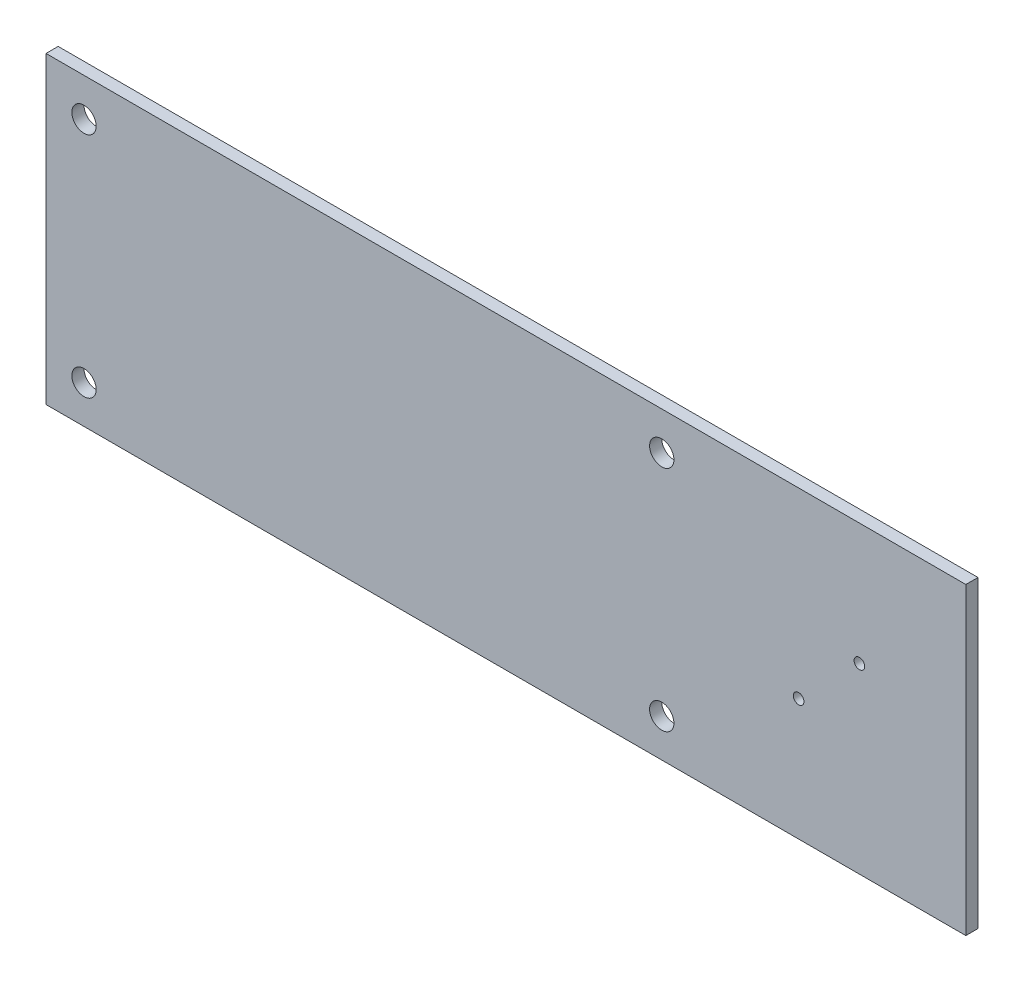
SolidWorks part; units mm, degrees
ref_plane "Plan de face" through (0, 0, 0) normal (0, 0, 1) x (1, 0, 0)
ref_plane "Plan de dessus" through (0, 0, 0) normal (0, 1, 0) x (1, 0, 0)
ref_plane "Plan de droite" through (0, 0, 0) normal (1, 0, 0) x (0, 0, -1)
sketch "Esquisse1" plane through (0, 0, 0) normal (0, 0, 1) x (1, 0, 0)
  line L0 (0, 20) -> (121, 20) construction
  line L1 (0, 0) -> (121, 0)
  line L2 (0, 0) -> (0, 40)
  line L3 (0, 40) -> (121, 40)
  line L4 (121, 0) -> (121, 40)
  line L5 (0, 5) -> (121, 5) construction
  line L6 (0, 35) -> (121, 35) construction
  line L7 (5, 0) -> (5, 40) construction
  line L8 (81, 0) -> (81, 40) construction
  line L9 (103, 0) -> (103, 40) construction
  line L10 (107, 0) -> (107, 40) construction
  line L11 (0, 16) -> (121, 16) construction
  line L12 (99, 0) -> (99, 40) construction
  line L13 (0, 24) -> (121, 24) construction
  circle A0 centre (5, 35) radius 1.6
  circle A1 centre (5, 5) radius 1.6
  circle A2 centre (81, 5) radius 1.6
  circle A3 centre (81, 35) radius 1.6
  circle A4 centre (107, 24) radius 0.7
  circle A5 centre (99, 16) radius 0.7
  point P25 (0, 18)
  point P26 (121, 18)
  point P27 (105, 0)
  point P28 (105, 40)
  point P29 (0, 22)
  point P30 (121, 22)
  point P31 (101, 0)
  point P32 (101, 40)
  dimension "D5" = 18
  dimension "D1" = 15
  dimension "D2" = 15
  dimension "D6" = 4
  dimension "D3" = 5
  dimension "D4" = 76
  dimension "D7" = 4
extrude "Boss.-Extru.1" add sketch "Esquisse1" along normal blind 1.6
